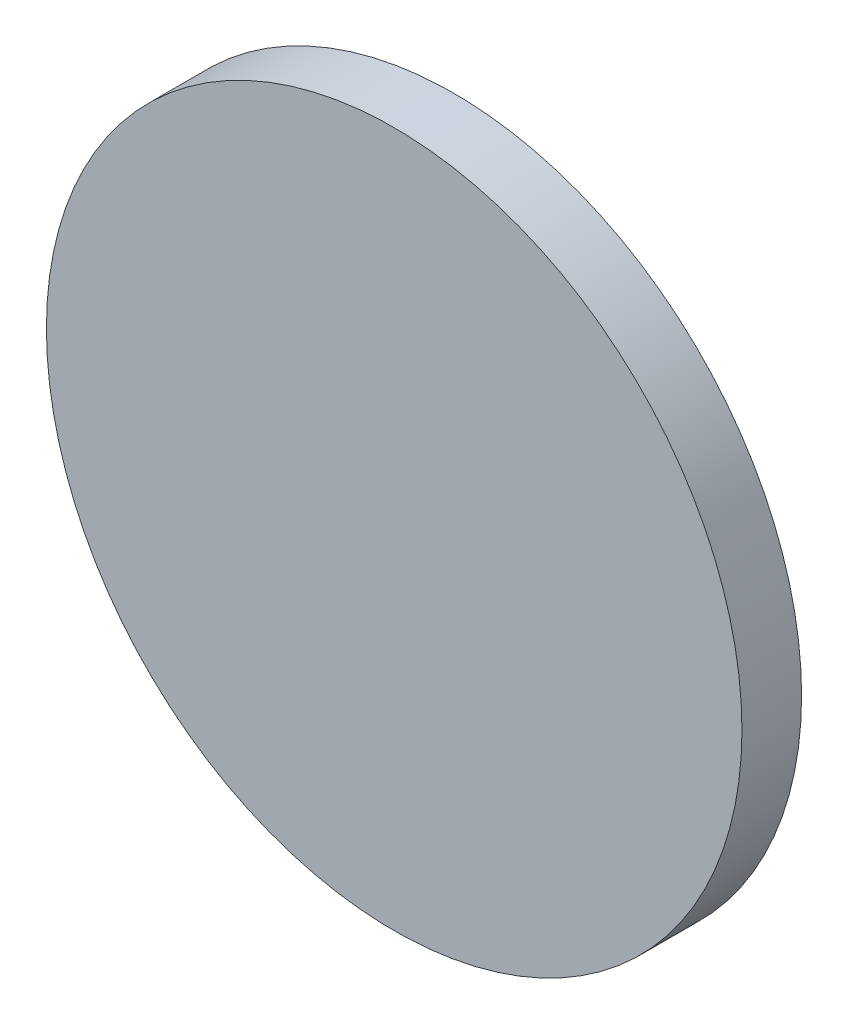
SolidWorks part; units mm, degrees
material "6061-T6 (SS)"
ref_plane "Front Plane" through (0, 0, 0) normal (0, 0, 1) x (1, 0, 0)
ref_plane "Top Plane" through (0, 0, 0) normal (0, 1, 0) x (1, 0, 0)
ref_plane "Right Plane" through (0, 0, 0) normal (1, 0, 0) x (0, 0, -1)
sketch "Sketch1" plane through (0, 0, 0) normal (1, 0, 0) x (0, 0, -1)
  line L0 (0, 0) -> (50000, 0) construction
  line L1 (0, 0) -> (0, 50000) construction
  line L2 (0, 66.675) -> (11.43, 66.675)
  line L3 (11.43, 66.675) -> (11.43, 63.5)
  line L4 (11.43, 63.5) -> (5.08, 63.5)
  line L5 (5.08, 63.5) -> (5.08, 0)
  line L6 (5.08, 0) -> (0, 0)
  line L7 (0, 0) -> (0, 66.675)
  dimension "D1" = 5.08
  dimension "D3" = 3.175
  dimension "D4" = 63.5
  dimension "D5" = 6.35
revolve "Revolve2" add sketch "Sketch1" angle 360 about L0
sketch "Sketch2" plane through (0, 0, 0) normal (0, 0, 1) x (1, 0, 0)
  line L0 (0, 69.6267) -> (0, -75.1511) construction
  line L1 (-114.4888, 0) -> (118.2987, 0) construction
  circle A0 centre (-31.75, 31.75) radius 5
  circle A1 centre (31.75, 31.75) radius 5
  circle A2 centre (31.75, -31.75) radius 5
  circle A3 centre (-31.75, -31.75) radius 5
  dimension "D1" = 10
  dimension "D2" = 31.75
  dimension "D3" = 31.75
extrude "Cut-Extrude1" [suppressed] cut sketch "Sketch2" against normal through all
